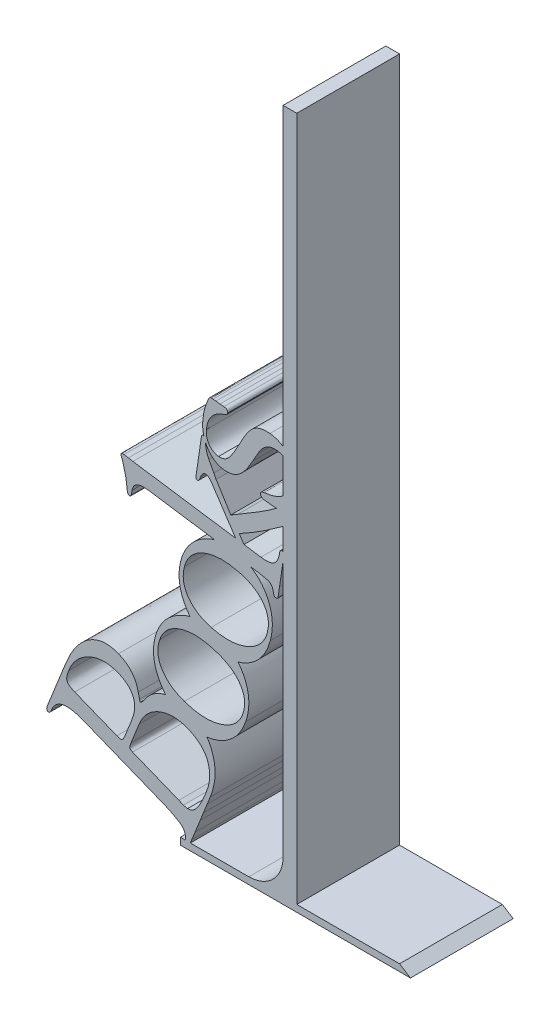
SolidWorks part; units mm, degrees
ref_plane "Plan de face" through (0, 0, 0) normal (0, 0, 1) x (1, 0, 0)
ref_plane "Plan de dessus" through (0, 0, 0) normal (0, 1, 0) x (1, 0, 0)
ref_plane "Plan de droite" through (0, 0, 0) normal (1, 0, 0) x (0, 0, -1)
sketch "Esquisse1" plane through (0, 0, 0) normal (0, 0, 1) x (1, 0, 0)
  line L0 (0, 0) -> (37.189, 0)
  line L1 (37.189, 0) -> (34, 2)
  line L2 (34, 2) -> (4, 2)
  line L3 (4, 2) -> (4, 202)
  line L4 (4, 202) -> (0, 202)
  line L5 (0, 202) -> (0, 2)
  line L6 (0, 2) -> (-30, 2)
  line L7 (-30, 2) -> (-30, 0)
  line L8 (-30, 0) -> (0, 0)
  point P12 (-4.9348, 202.4719)
  dimension "D1" = 2
  dimension "D2" = 4
  dimension "D3" = 2
  dimension "100" = 200
  dimension "D4" = 30
  dimension "D5" = 30
sketch "Esquisse3" plane through (0, 0, 0) normal (0, 0, 1) x (1, 0, 0)
  line L3 (-29.24, -3.4331) -> (4, 68.1983) construction
  line L6 (4, 68.1983) -> (4, 122.6014) construction
  line L8 (4, 2) -> (4, 202) construction
  spline S0 degree 2 poles (-29.24, -3.4331) (4, 68.1983) (4, 122.6014) knots 0 0 0 1 1 1 construction
  text T0 "Books" font "Goudy Old Style" height 45
  point P0 (4, 122.6014)
  point P2 (2, 28.5567)
extrude "Boss.-Extru.1" add sketch "Esquisse1" along normal blind 30
extrude "Boss.-Extru.2" add sketch "Esquisse3" along normal blind 30
fillet "Congé1" radius 10 1 edges at (0, 2, 15)
